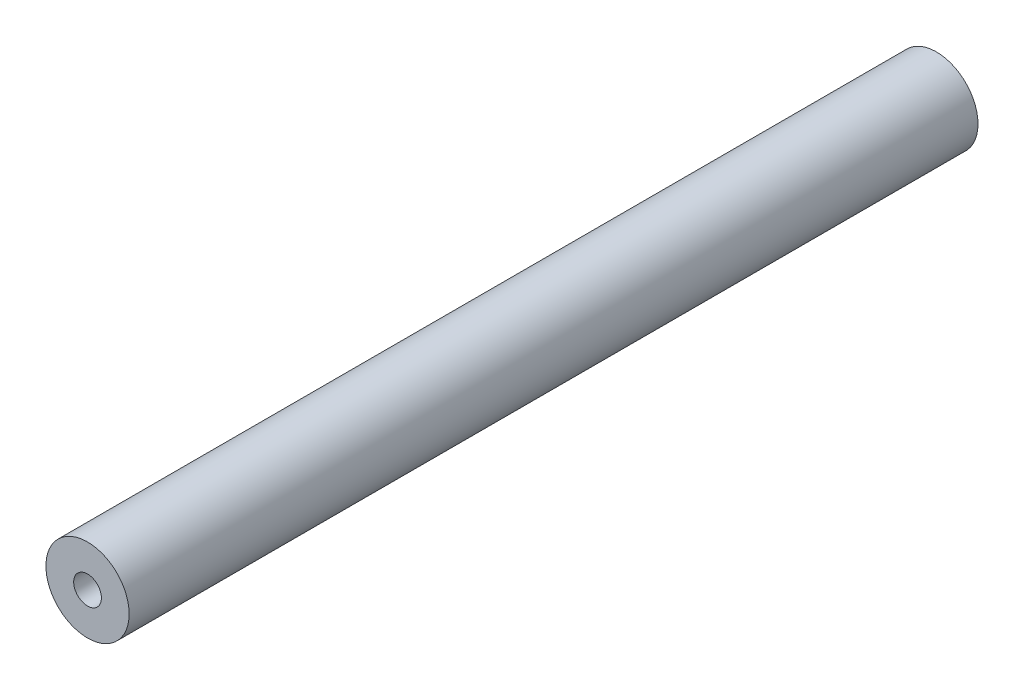
SolidWorks part; units mm, degrees
material "ABS"
ref_plane "Front Plane" through (0, 0, 0) normal (0, 0, 1) x (1, 0, 0)
ref_plane "Top Plane" through (0, 0, 0) normal (0, 1, 0) x (1, 0, 0)
ref_plane "Right Plane" through (0, 0, 0) normal (1, 0, 0) x (0, 0, -1)
sketch "Sketch1" plane through (0, 0, 0) normal (0, 0, 1) x (1, 0, 0)
  circle A0 centre (0, 0) radius 38.1
  circle A1 centre (0, 0) radius 12.7
  dimension "D1" = 76.2
  dimension "D2" = 25.4
extrude "Boss-Extrude1" add sketch "Sketch1" along normal blind 777.24
